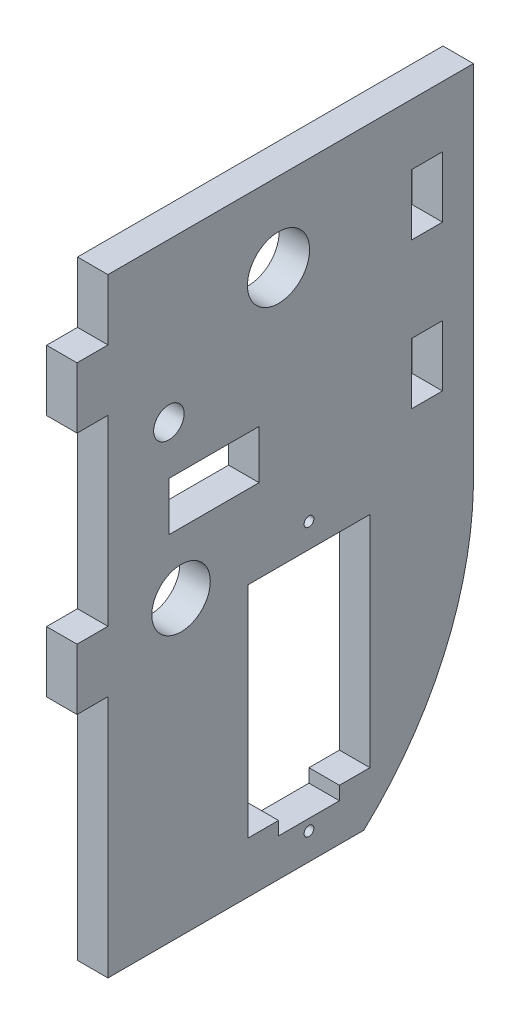
SolidWorks part; units mm, degrees
ref_plane "Front Plane" through (0, 0, 0) normal (0, 0, 1) x (1, 0, 0)
ref_plane "Top Plane" through (0, 0, 0) normal (0, 1, 0) x (1, 0, 0)
ref_plane "Right Plane" through (0, 0, 0) normal (1, 0, 0) x (0, 0, -1)
sketch "Sketch1" plane through (0, 0, 0) normal (1, 0, 0) x (0, 0, -1)
  line L1 (-19.05, -31.75) -> (19.05, -31.75)
  line L2 (-19.05, -31.75) -> (-19.05, 31.75)
  line L3 (-19.05, 31.75) -> (19.05, 31.75)
  line L4 (19.05, -31.75) -> (19.05, 31.75)
  line L5 (-19.05, -31.75) -> (19.05, 31.75) construction
  line L6 (-19.05, 31.75) -> (19.05, -31.75) construction
  point P0 (0, 0)
  dimension "D1" = 63.5
  dimension "D2" = 38.1
extrude "main body" add sketch "Sketch1" along normal blind 3.175
sketch "Sketch2" plane through (3.175, 0, 0) normal (1, 0, 0) x (0, 0, -1)
  line L0 (-19.05, 25.4) -> (-22.2758, 25.4)
  line L1 (-19.05, 31.75) -> (-19.05, -31.75) construction
  line L2 (-22.2758, 25.4) -> (-22.2758, 19.05)
  line L3 (-22.2758, 19.05) -> (-19.05, 19.05)
  line L4 (-19.05, 19.05) -> (-19.05, 25.4)
  line L5 (19.05, 31.75) -> (-19.05, 31.75) construction
  line L6 (-19.05, -6.35) -> (-22.2758, -6.35)
  line L7 (-22.2758, -6.35) -> (-22.2758, 0)
  line L8 (-22.2758, 0) -> (-19.05, 0)
  line L9 (-19.05, 0) -> (-19.05, -6.35)
  dimension "D1" = 3.2258
  dimension "D2" = 6.35
  dimension "D3" = 6.35
  dimension "D4" = 3.2258
  dimension "D5" = 6.35
  dimension "D6" = 19.05
extrude "tabs" add sketch "Sketch2" against normal blind 3.175
sketch "Sketch5" plane through (3.175, 0, 0) normal (1, 0, 0) x (0, 0, -1)
  line L0 (-19.05, -31.75) -> (19.05, -31.75) construction
  line L1 (-19.05, -6.35) -> (-19.05, -31.75) construction
  line B0 (8.255, -3.556) -> (-4.445, -3.556)
  line B1 (8.255, -3.556) -> (8.255, -26.416)
  line B2 (8.255, -26.416) -> (5.08, -26.416)
  line B3 (-4.445, -3.556) -> (-4.445, -26.416)
  line B4 (5.08, -26.416) -> (5.08, -27.813)
  line B5 (5.08, -27.813) -> (-1.27, -27.813)
  line B6 (-1.27, -26.416) -> (-1.27, -27.813)
  line B7 (-1.27, -26.416) -> (-4.445, -26.416)
  circle B8 centre (1.905, -28.956) radius 0.508
  circle B9 centre (1.905, -1.016) radius 0.508
  dimension "D1" = 11.43
  dimension "D2" = 20.955
sketch_block_instance "servo_hole_SG90-1"
sketch_block "servo_hole_SG90" parameters "D5"=1.016, "D6"=1.016, "D9"=2.1092, "D1"=27.94, "D2"=6.35, "D3"=22.86, "D4"=12.7, "D7"=1.397, "D8"=6.35
extrude "motor cut" cut sketch "Sketch5" against normal through all
sketch "Sketch6" plane through (3.175, 0, 0) normal (1, 0, 0) x (0, 0, -1)
  line L0 (-19.05, 31.75) -> (-19.05, 25.4) construction
  line L1 (19.05, 31.75) -> (-19.05, 31.75) construction
  circle A0 centre (-1.27, 23.495) radius 3.2385
  dimension "D3" = 6.477
  dimension "D1" = 17.78
  dimension "D2" = 8.255
extrude "cut for axle" cut sketch "Sketch6" against normal through all
sketch "Sketch7" plane through (3.175, 0, 0) normal (1, 0, 0) x (0, 0, -1)
  line L0 (19.05, -31.75) -> (19.05, -6.35)
  line L1 (19.05, -31.75) -> (19.05, 31.75) construction
  line L2 (19.05, -31.75) -> (7.62, -31.75)
  line L4 (-19.05, -31.75) -> (19.05, -31.75) construction
  arc A0 (19.05, -6.35) -> (7.62, -31.75) centre (-16.5026, -5.6231) cw
  dimension "D1" = 25.4
  dimension "D2" = 11.43
extrude "round off back corner" cut sketch "Sketch7" against normal through all
sketch "Sketch8" plane through (3.175, 0, 0) normal (1, 0, 0) x (0, 0, -1)
  line L0 (14.2113, 22.225) -> (14.2113, 6.985) construction
  line L1 (12.5984, 19.05) -> (15.8242, 19.05)
  line L2 (12.5984, 19.05) -> (12.5984, 25.4)
  line L3 (12.5984, 25.4) -> (15.8242, 25.4)
  line L4 (15.8242, 19.05) -> (15.8242, 25.4)
  line L5 (12.5984, 19.05) -> (15.8242, 25.4) construction
  line L6 (12.5984, 25.4) -> (15.8242, 19.05) construction
  line L7 (12.5984, 3.81) -> (15.8242, 3.81)
  line L8 (12.5984, 3.81) -> (12.5984, 10.16)
  line L9 (12.5984, 10.16) -> (15.8242, 10.16)
  line L10 (15.8242, 3.81) -> (15.8242, 10.16)
  line L11 (12.5984, 3.81) -> (15.8242, 10.16) construction
  line L12 (12.5984, 10.16) -> (15.8242, 3.81) construction
  line L13 (19.05, 31.75) -> (-19.05, 31.75) construction
  line L14 (19.05, -6.35) -> (19.05, 31.75) construction
  point P0 (14.2113, 22.225)
  point P5 (14.2113, 6.985)
  dimension "D1" = 8.89
  dimension "D2" = 6.35
  dimension "D3" = 3.2258
  dimension "D4" = 6.35
  dimension "D5" = 6.35
  dimension "D6" = 3.2258
  dimension "D7" = 3.2258
extrude "cut for tabs" cut sketch "Sketch8" against normal through all
sketch "Sketch9" plane through (3.175, 0, 0) normal (1, 0, 0) x (0, 0, -1)
  line L0 (-19.05, 19.05) -> (-19.05, 0) construction
  line L1 (19.05, 31.75) -> (-19.05, 31.75) construction
  circle A0 centre (-12.7, 15.24) radius 1.5875
  dimension "D1" = 3.175
  dimension "D2" = 6.35
  dimension "D3" = 16.51
extrude "cut for bracket screw" cut sketch "Sketch9" against normal through all
sketch "Sketch10" plane through (3.175, 0, 0) normal (1, 0, 0) x (0, 0, -1)
  line L0 (-19.05, -31.75) -> (7.62, -31.75) construction
  line L1 (-19.05, 19.05) -> (-19.05, 0) construction
  circle A0 centre (-11.43, -1.27) radius 3.048
  dimension "D3" = 6.096
  dimension "D1" = 30.48
  dimension "D2" = 7.62
extrude "cut for basic 2nd mount axle" cut sketch "Sketch10" against normal through all
sketch "Sketch11" plane through (3.175, 0, 0) normal (1, 0, 0) x (0, 0, -1)
  line L1 (-12.7, 10.171) -> (-3.302, 10.171)
  line L2 (-12.7, 10.171) -> (-12.7, 5.091)
  line L3 (-12.7, 5.091) -> (-3.302, 5.091)
  line L4 (-3.302, 10.171) -> (-3.302, 5.091)
  line L5 (-12.7, 10.171) -> (-3.302, 5.091) construction
  line L6 (-12.7, 5.091) -> (-3.302, 10.171) construction
  line L8 (-19.05, 19.05) -> (-19.05, 0) construction
  point P0 (-8.001, 7.631)
  dimension "D1" = 9.398
  dimension "D2" = 5.08
  dimension "D3" = 6.35
extrude "Cut-Extrude1" cut sketch "Sketch11" against normal through all
